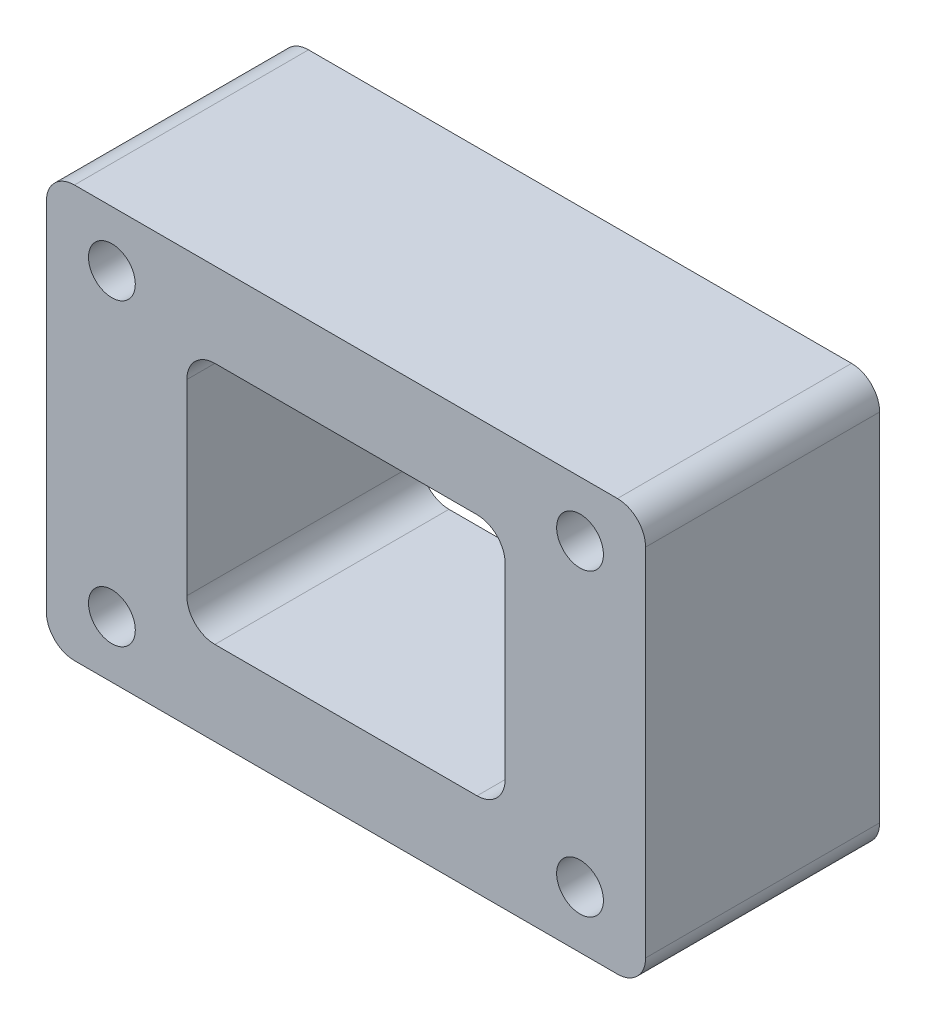
SolidWorks part; units mm, degrees
ref_plane "前视基准面" through (0, 0, 0) normal (0, 0, 1) x (1, 0, 0)
ref_plane "上视基准面" through (0, 0, 0) normal (0, 1, 0) x (1, 0, 0)
ref_plane "右视基准面" through (0, 0, 0) normal (1, 0, 0) x (0, 0, -1)
sketch "草图1" plane through (0, 0, 0) normal (0, 0, 1) x (1, 0, 0)
  line L1 (-32, 22) -> (32, 22)
  line L2 (-32, 22) -> (-32, -22)
  line L3 (-32, -22) -> (32, -22)
  line L4 (32, 22) -> (32, -22)
  line L5 (-32, 22) -> (32, -22) construction
  line L6 (-32, -22) -> (32, 22) construction
  line L7 (-17, 13) -> (17, 13)
  line L8 (-17, 13) -> (-17, -13)
  line L9 (-17, -13) -> (17, -13)
  line L10 (17, 13) -> (17, -13)
  line L11 (-17, 13) -> (17, -13) construction
  line L12 (-17, -13) -> (17, 13) construction
  circle A0 centre (-25, 16.0678) radius 2.5
  circle A1 centre (-25, -15.9322) radius 2.5
  circle A2 centre (25, -15.9322) radius 2.5
  circle A3 centre (25, 16.0678) radius 2.5
  point P0 (0, 0)
  point P10 (0, 0)
  dimension "D4" = 5
  dimension "D5" = 5
  dimension "D1" = 32
  dimension "D2" = 25
  dimension "D3" = 64
  dimension "D6" = 44
  dimension "D7" = 34
  dimension "D8" = 26
extrude "凸台-拉伸1" add sketch "草图1" along normal blind 25
fillet "圆角1" radius 3 8 edges at (17, -13, 12.5) (17, 13, 12.5) (-17, -13, 12.5) (-17, 13, 12.5) (-32, -22, 12.5) (-32, 22, 12.5) (32, -22, 12.5) (32, 22, 12.5)
